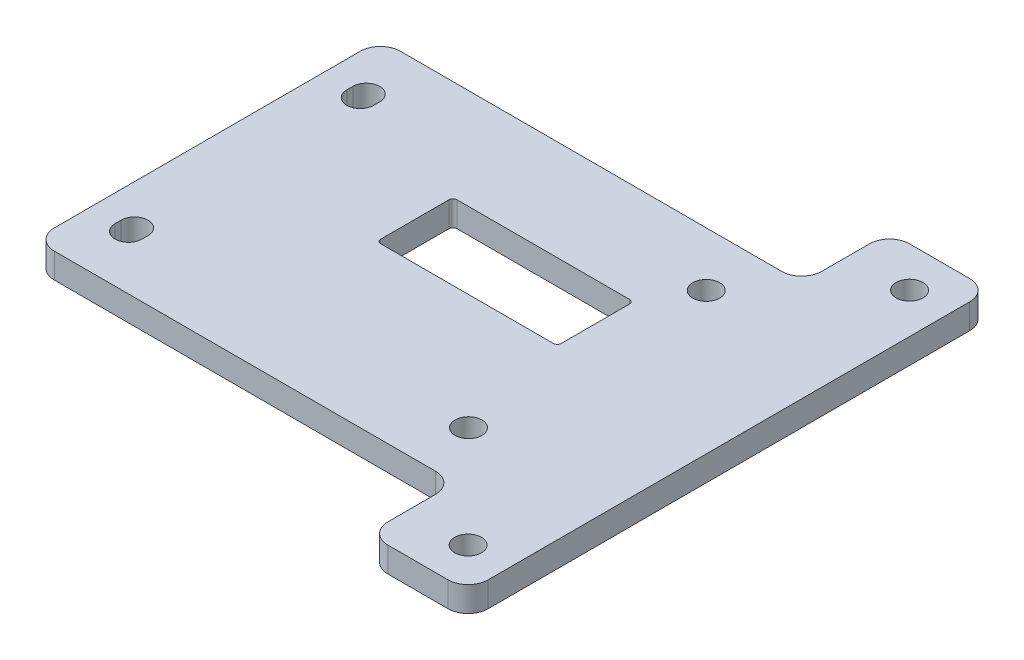
SolidWorks part; units mm, degrees
ref_plane "Front Plane" through (0, 0, 0) normal (0, 0, 1) x (1, 0, 0)
ref_plane "Top Plane" through (0, 0, 0) normal (0, 1, 0) x (1, 0, 0)
ref_plane "Right Plane" through (0, 0, 0) normal (1, 0, 0) x (0, 0, -1)
sketch "Sketch1" plane through (0, 0, 0) normal (0, 1, 0) x (1, 0, 0)
  line L1 (0, 0) -> (66.04, 0)
  line L2 (0, 0) -> (0, 43.815)
  line L3 (0, 43.815) -> (66.04, 43.815)
  line L4 (66.04, 0) -> (66.04, 43.815)
  dimension "D1" = 43.815
  dimension "D2" = 66.04
extrude "Boss-Extrude1" add sketch "Sketch1" along normal blind 3.175
sketch "Sketch3" plane through (0, 0, 0) normal (0, -1, 0) x (-1, 0, 0)
  line L0 (0, 21.9075) -> (-66.04, 21.9075) construction
  line L1 (0, 43.815) -> (0, 0) construction
  line L2 (-66.04, 0) -> (-66.04, 43.815) construction
  point P0 (-5.08, 6.858)
  point P1 (-48.1203, 6.858)
  point P2 (-60.96, 6.858)
  point P9 (-60.96, 36.957)
  point P10 (-48.1203, 36.957)
  point P11 (-5.08, 36.957)
  dimension "D1" = 30.099
  dimension "D2" = 43.0403
  dimension "D3" = 55.88
  dimension "D4" = 5.08
hole_wizard "M3 Clearance Hole1" positions "Sketch5" profile "Sketch4" hole size "M3" standard "ANSI Metric" end condition through all
sketch "Sketch5" plane through (0, 0, 0) normal (0, -1, 0) x (-1, 0, 0)
  point P0 (-5.08, 6.858)
  point P3 (-5.08, 36.957)
  point P6 (-48.1203, 36.957)
  point P9 (-48.1203, 6.858)
  point P12 (-60.96, 6.858)
  point P15 (-60.96, 36.957)
sketch "Sketch4" plane through (5.08, 0, -6.858) normal (1, 0, 0) x (0, 0, -1)
  line L0 (0, 0) -> (0, 3.175)
  line L1 (0, 3.175) -> (1.7, 3.175)
  line L2 (1.7, 3.175) -> (1.7, 0)
  line L5 (1.7, 0) -> (0, 0)
  line L11 (0, -6.35) -> (0, 107.95) construction
  dimension "Thru Hole Dia." = 3.4
  dimension "Thru Hole Depth" = 3.175
sketch "Sketch6" plane through (0, 3.175, 0) normal (0, 1, 0) x (1, 0, 0)
  line L22 (44.7548, 21.463) -> (44.7548, 31.115)
  line L23 (44.7548, 31.115) -> (21.8948, 31.115)
  line L24 (21.8948, 31.115) -> (21.8948, 21.463)
  line L25 (21.8948, 21.463) -> (44.7548, 21.463)
  line L26 (44.7548, 21.463) -> (44.7548, 31.115)
  line L27 (44.7548, 31.115) -> (21.8948, 31.115)
  line L28 (21.8948, 31.115) -> (21.8948, 21.463)
  line L29 (21.8948, 21.463) -> (44.7548, 21.463)
  dimension "D1" = 1.27
extrude "Cut-Extrude1" cut sketch "Sketch6" against normal through all
fillet "Fillet1" radius 0.508 4 edges at (44.7548, 1.5875, -31.115) (44.7548, 1.5875, -21.463) (21.8948, 1.5875, -21.463) (21.8948, 1.5875, -31.115)
fillet "Fillet2" radius 2.54 4 edges at (0, 1.5875, -43.815) (66.04, 1.5875, -43.815) (66.04, 1.5875, 0) (0, 1.5875, 0)
sketch "Sketch7" plane through (0, 3.175, 0) normal (0, 1, 0) x (1, 0, 0)
  line L4 (66.04, 54.9275) -> (53.34, 54.9275)
  line L5 (66.04, 54.9275) -> (66.04, -11.1125)
  line L6 (66.04, -11.1125) -> (53.34, -11.1125)
  line L7 (53.34, 54.9275) -> (53.34, -11.1125)
  line L8 (66.04, 21.9075) -> (87.9877, 21.9075) construction
  line L9 (66.04, 2.54) -> (66.04, 41.275) construction
  line L10 (60.96, 36.957) -> (48.1203, 36.957) construction
  dimension "D1" = 12.7
  dimension "D2" = 66.04
extrude "Boss-Extrude2" add sketch "Sketch7" against normal up to surface (3.175 mm away) up to face at (33.3248, 0, -26.289)
sketch "Sketch8" plane through (0, 3.175, 0) normal (0, 1, 0) x (1, 0, 0)
  line L0 (66.04, 21.9075) -> (52.6686, 21.9075) construction
  line L1 (0, 21.9075) -> (66.04, 21.9075) construction
  point P0 (60.96, 49.8475)
  point P6 (60.96, -6.0325)
  dimension "D1" = 27.94
hole_wizard "M3 Clearance Hole2" positions "Sketch10" profile "Sketch9" hole size "M3" standard "ANSI Metric" end condition through all
sketch "Sketch10" plane through (0, 3.175, 0) normal (0, 1, 0) x (1, 0, 0)
  point P0 (60.96, 49.8475)
  point P3 (60.96, -6.0325)
sketch "Sketch9" plane through (60.96, 3.175, -49.8475) normal (1, 0, 0) x (0, 0, 1)
  line L0 (0, 0) -> (0, 3.175)
  line L1 (0, 3.175) -> (1.7, 3.175)
  line L2 (1.7, 3.175) -> (1.7, 0)
  line L5 (1.7, 0) -> (0, 0)
  line L11 (0, -6.35) -> (0, 107.95) construction
  dimension "Thru Hole Dia." = 3.4
  dimension "Thru Hole Depth" = 3.175
fillet "Fillet3" radius 2.54 6 edges at (66.04, 1.5875, 11.1125) (53.34, 1.5875, 11.1125) (53.34, 1.5875, 0) (66.04, 1.5875, -54.9275) (53.34, 1.5875, -54.9275) (53.34, 1.5875, -43.815)
sketch "Sketch11" plane through (0, 0, 0) normal (0, -1, 0) x (1, 0, 0)
  line L0 (0, -21.9075) -> (77.791, -21.9075) construction
  line L1 (3.38, -6.858) -> (3.38, -7.62)
  line L2 (6.78, -7.62) -> (6.78, -6.858)
  line L3 (6.78, -36.195) -> (6.78, -36.957)
  line L4 (3.38, -36.957) -> (3.38, -36.195)
  circle A0 centre (5.08, -6.858) radius 1.7 construction
  arc A1 (3.38, -7.62) -> (6.78, -7.62) centre (5.08, -7.62) ccw
  arc A2 (3.38, -6.858) -> (6.78, -6.858) centre (5.08, -6.858) cw
  arc A3 (3.38, -36.195) -> (6.78, -36.195) centre (5.08, -36.195) cw
  arc A4 (3.38, -36.957) -> (6.78, -36.957) centre (5.08, -36.957) ccw
  dimension "D1" = 28.575
extrude "Cut-Extrude2" cut sketch "Sketch11" against normal through all
